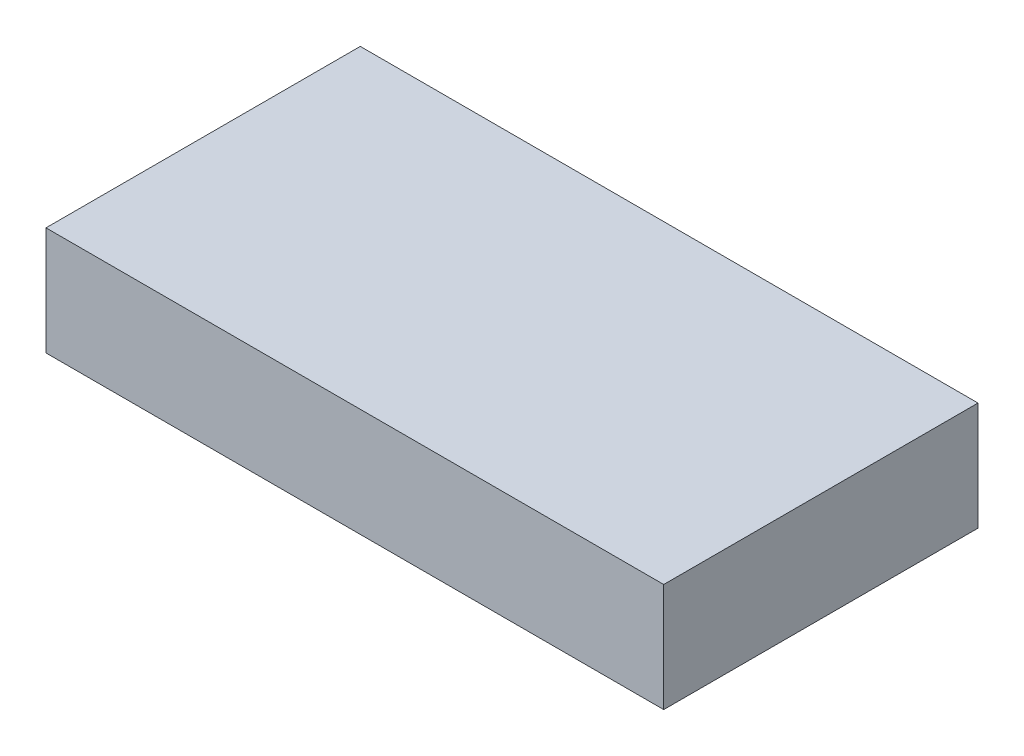
SolidWorks part; units mm, degrees
ref_plane "Front Plane" through (0, 0, 0) normal (0, 0, 1) x (1, 0, 0)
ref_plane "Top Plane" through (0, 0, 0) normal (0, 1, 0) x (1, 0, 0)
ref_plane "Right Plane" through (0, 0, 0) normal (1, 0, 0) x (0, 0, -1)
sketch "Sketch1" plane through (0, 0, 0) normal (0, 1, 0) x (1, 0, 0)
  line L1 (0, 0) -> (57, 0)
  line L2 (0, 0) -> (0, 29)
  line L3 (0, 29) -> (57, 29)
  line L4 (57, 0) -> (57, 29)
  dimension "D1" = 57
  dimension "D2" = 29
extrude "Boss-Extrude1" add sketch "Sketch1" along normal blind 10
